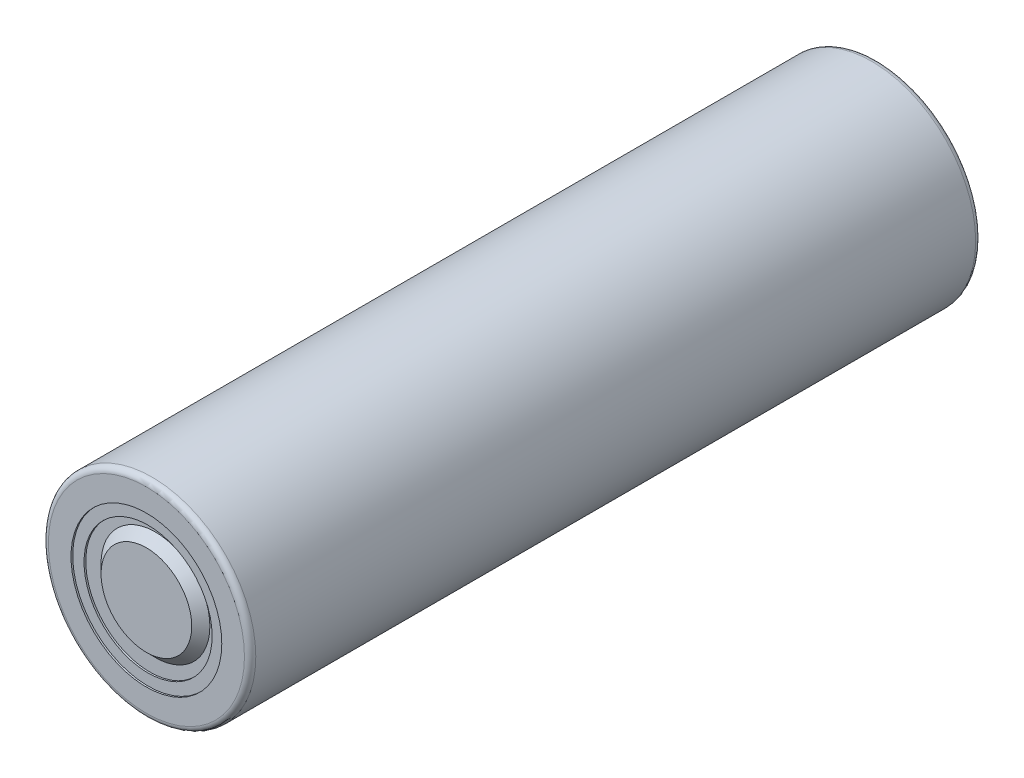
SolidWorks part; units mm, degrees
ref_plane "Front Plane" through (0, 0, 0) normal (0, 0, 1) x (1, 0, 0)
ref_plane "Top Plane" through (0, 0, 0) normal (0, 1, 0) x (1, 0, 0)
ref_plane "Right Plane" through (0, 0, 0) normal (1, 0, 0) x (0, 0, -1)
sketch "Sketch1" plane through (0, 0, 0) normal (0, 0, 1) x (1, 0, 0)
  circle A0 centre (0, 0) radius 9.15
  dimension "D1" = 18.3
extrude "Boss-Extrude1" add sketch "Sketch1" along normal blind 64.5
sketch "Sketch2" plane through (0, 0, 0) normal (0, 0, 1) x (1, 0, 0)
  circle A0 centre (0, 0) radius 7.15
extrude "Cut-Extrude1" cut sketch "Sketch2" along normal blind 0.2
sketch "Sketch3" plane through (0, 0, 0) normal (0, 1, 0) x (1, 0, 0)
  line L16 (0, -64.8359) -> (0, -63.0858) construction
  line L17 (-8.15, -64.2) -> (-8.15, -63.7)
  line L18 (-4.8, -63.7) -> (-4, -64.5)
  line L19 (-4, -64.5) -> (-6.65, -64.5)
  line L20 (-6.65, -64.5) -> (-6.65, -64.35)
  line L21 (-6.65, -64.35) -> (-5.65, -64.35)
  line L22 (-5.65, -64.35) -> (-5.65, -64.2)
  line L23 (-5.65, -64.2) -> (-8.15, -64.2)
  line L24 (-8.15, -63.7) -> (-4.8, -63.7)
revolve "Cut-Revolve1" cut sketch "Sketch3" angle 360 about L16
fillet "Fillet1" radius 0.5 2 edges at (9.15, 0, 0) (9.15, 0, 64.5)
